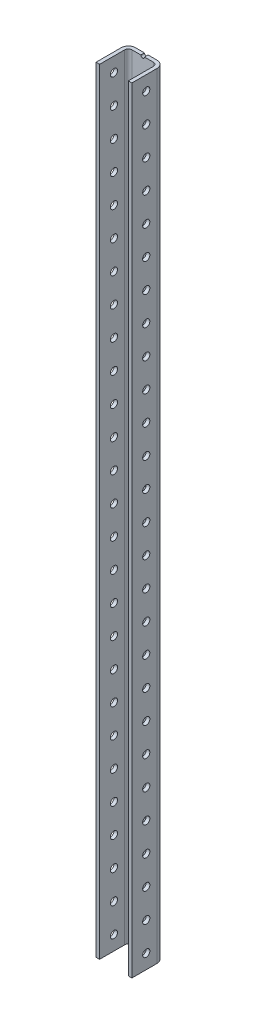
SolidWorks part; units mm, degrees
material "5052-O"
ref_plane "Front Plane" through (0, 0, 0) normal (0, 0, 1) x (1, 0, 0)
ref_plane "Top Plane" through (0, 0, 0) normal (0, 1, 0) x (1, 0, 0)
ref_plane "Rithe Plane" through (0, 0, 0) normal (1, 0, 0) x (0, 0, -1)
sketch "Sketch1" plane through (0, 0, 0) normal (0, 1, 0) x (1, 0, 0)
  line L0 (0, 103.632) -> (0, -110.3752) construction
  line L1 (-12.7, 0) -> (-12.7, 22.225)
  line L2 (-9.525, 25.4) -> (9.525, 25.4)
  line L3 (12.7, 22.225) -> (12.7, 0)
  line L4 (12.7, 0) -> (15.875, 0)
  line L5 (15.875, 0) -> (15.875, 22.225)
  line L6 (9.525, 28.575) -> (-9.525, 28.575)
  line L7 (-15.875, 22.225) -> (-15.875, 0)
  line L8 (-15.875, 0) -> (-12.7, 0)
  arc A0 (-12.7, 22.225) -> (-9.525, 25.4) centre (-9.525, 22.225) cw
  arc A1 (12.7, 22.225) -> (9.525, 25.4) centre (9.525, 22.225) ccw
  arc A2 (9.525, 28.575) -> (15.875, 22.225) centre (9.525, 22.225) cw
  arc A3 (-15.875, 22.225) -> (-9.525, 28.575) centre (-9.525, 22.225) cw
  dimension "D5" = 3.175
  dimension "D6" = 6.35
  dimension "D1" = 31.75
  dimension "D2" = 25.4
  dimension "D3" = 28.575
  dimension "D4" = 25.4
extrude "Extrude1" add sketch "Sketch1" along normal mid plane 685.8
sketch "Sketch2" plane through (0, 0, -28.575) normal (0, 0, -1) x (-1, 0, 0)
  line L0 (0, 461.5657) -> (0, -466.4615) construction
  line L1 (9.525, 342.9) -> (-9.525, 342.9) construction
  line L2 (-9.525, -342.9) -> (9.525, -342.9) construction
  line L4 (-9.525, 342.9) -> (9.525, 342.9) construction
  circle A0 centre (0, 342.9) radius 1.5876
  circle A1 centre (-1.905, 209.55) radius 4.826
  circle A2 centre (-1.905, 184.15) radius 4.826
  circle A3 centre (-1.905, -6.35) radius 4.826
  circle A5 centre (1.905, 101.6) radius 4.826
  circle A6 centre (-1.905, -260.35) radius 4.826
  circle A7 centre (-1.905, -234.95) radius 4.826
  circle A11 centre (-1.905, 19.05) radius 4.826
  dimension "D1" = 3.1752
  dimension "D2" = 9.652
  dimension "D6" = 82.55
  dimension "D10" = 25.4
  dimension "D8" = 82.55
  dimension "D3" = 1.905
  dimension "D4" = 133.35
  dimension "D5" = 25.4
  dimension "D9" = 1.905
  dimension "D12" = 82.55
  dimension "D13" = 25.4
extrude "Extrude2" cut sketch "Sketch2" against normal blind 25
hole_wizard "1/4 (0.25) Diameter Hole1" positions "Sketch4" profile "Sketch3" hole size "1/4" standard "Ansi Inch" end condition through all
sketch "Sketch4" plane through (-15.875, 0, 0) normal (-1, 0, 0) x (0, 0, 1)
  line L0 (-22.225, 342.9) -> (0, 342.9) construction
  line L1 (0, 342.9) -> (0, -342.9) construction
  point P0 (-12.7, 330.2)
  dimension "D1" = 12.7
  dimension "D2" = 12.7
sketch "Sketch3" plane through (-15.875, 330.2, -12.7) normal (0, 1, 0) x (0, 0, 1)
  line L0 (0, 0) -> (0, 31.75)
  line L1 (0, 31.75) -> (3.175, 31.75)
  line L2 (3.175, 31.75) -> (3.175, 0)
  line L5 (3.175, 0) -> (0, 0)
  line L11 (0, -6.35) -> (0, 107.95) construction
  dimension "Thru Hole Dia." = 6.35
  dimension "Thru Hole Depth" = 31.75
pattern_linear "LPattern1" count 27 spacing 25.4 along (0, -1, 0) of "1/4 (0.25) Diameter Hole1"
sketch "Sketch5" [suppressed] plane through (-15.875, 0, 0) normal (-1, 0, 0) x (0, 0, 1)
  line L0 (-28.575, 342.9) -> (-28.575, -342.9) construction
  line L1 (0, 342.9) -> (-28.575, 342.9)
  line L2 (0, 342.9) -> (0, 292.1)
  line L3 (0, 292.1) -> (-28.575, 292.1)
  line L4 (-28.575, 342.9) -> (-28.575, 292.1)
  dimension "D1" = 50.8
extrude "Extrude3" [suppressed] cut sketch "Sketch5" against normal through all
